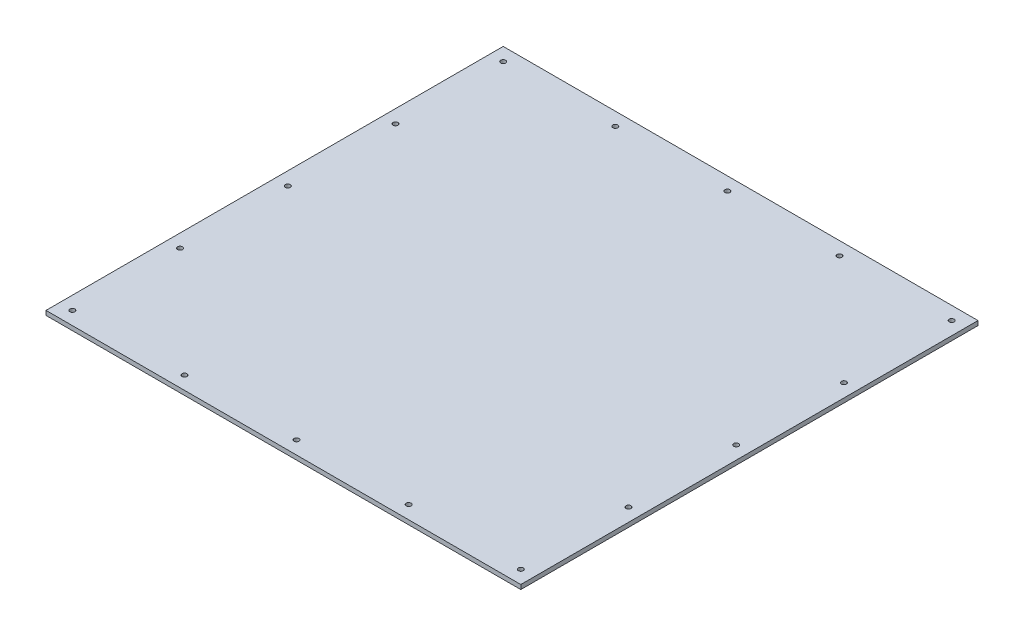
SolidWorks part; units mm, degrees
material "6061 Alloy"
ref_plane "Front Plane" through (0, 0, 0) normal (0, 0, 1) x (1, 0, 0)
ref_plane "Top Plane" through (0, 0, 0) normal (0, 1, 0) x (1, 0, 0)
ref_plane "Right Plane" through (0, 0, 0) normal (1, 0, 0) x (0, 0, -1)
sketch "8020 Reference" plane through (0, 0, 0) normal (0, 1, 0) x (1, 0, 0)
  line L0 (647.7, 0) -> (685.8, 0) construction
  line L1 (0, 0) -> (38.1, 0) construction
  line L2 (0, 0) -> (0, -38.1) construction
  line L3 (0, -38.1) -> (38.1, -38.1) construction
  line L4 (38.1, 0) -> (38.1, -38.1) construction
  line L5 (647.7, 0) -> (647.7, -38.1) construction
  line L6 (647.7, -38.1) -> (685.8, -38.1) construction
  line L7 (685.8, 0) -> (685.8, -38.1) construction
  line L8 (0, -622.3) -> (38.1, -622.3) construction
  line L9 (0, -622.3) -> (0, -660.4) construction
  line L10 (0, -660.4) -> (38.1, -660.4) construction
  line L11 (38.1, -622.3) -> (38.1, -660.4) construction
  line L12 (647.7, -622.3) -> (685.8, -622.3) construction
  line L13 (647.7, -622.3) -> (647.7, -660.4) construction
  line L14 (647.7, -660.4) -> (685.8, -660.4) construction
  line L15 (685.8, -622.3) -> (685.8, -660.4) construction
  circle A0 centre (19.05, -19.05) radius 3.57 construction
  circle A1 centre (666.75, -19.05) radius 3.57 construction
  circle A2 centre (19.05, -641.35) radius 3.57 construction
  circle A3 centre (666.75, -641.35) radius 3.57 construction
  point P8 (19.05, 0)
  point P9 (0, -19.05)
  point P15 (666.75, 0)
  point P16 (647.7, -19.05)
  point P24 (19.05, -622.3)
  point P25 (0, -641.35)
  point P32 (666.75, -622.3)
  point P33 (647.7, -641.35)
  dimension "D2" = 7.14
  dimension "D4" = 7.14
  dimension "D7" = 7.14
  dimension "D9" = 7.14
  dimension "D1" = 38.1
  dimension "D3" = 38.1
  dimension "D5" = 685.8
  dimension "D6" = 38.1
  dimension "D8" = 38.1
  dimension "D10" = 660.4
sketch "Sketch2" plane through (0, 0, 0) normal (0, 1, 0) x (1, 0, 0)
  line L0 (19.05, -19.05) -> (19.05, -641.35) construction
  line L1 (0, 0) -> (685.8, 0)
  line L2 (0, 0) -> (0, -660.4)
  line L3 (0, -660.4) -> (685.8, -660.4)
  line L4 (685.8, 0) -> (685.8, -660.4)
  line L5 (19.05, -641.35) -> (666.75, -641.35) construction
  line L6 (666.75, -641.35) -> (666.75, -19.05) construction
  line L7 (666.75, -19.05) -> (19.05, -19.05) construction
  line L8 (180.975, -19.05) -> (180.975, -641.35) construction
  line L9 (19.05, -174.625) -> (666.75, -174.625) construction
  line L10 (666.75, -485.775) -> (19.05, -485.775) construction
  line L11 (504.825, -19.05) -> (504.825, -641.35) construction
  line L12 (342.9, -19.05) -> (19.05, -19.05) construction
  circle A0 centre (19.05, -19.05) radius 3.57
  circle A1 centre (666.75, -19.05) radius 3.57
  circle A2 centre (666.75, -641.35) radius 3.57
  circle A3 centre (19.05, -641.35) radius 3.57
  circle A4 centre (342.9, -19.05) radius 3.57
  circle A5 centre (19.05, -330.2) radius 3.57
  circle A6 centre (342.9, -641.35) radius 3.57
  circle A7 centre (666.75, -330.2) radius 3.57
  circle A8 centre (180.975, -19.05) radius 3.57
  circle A9 centre (504.825, -19.05) radius 3.57
  circle A10 centre (666.75, -174.625) radius 3.57
  circle A11 centre (19.05, -174.625) radius 3.57
  circle A12 centre (19.05, -485.775) radius 3.57
  circle A13 centre (666.75, -485.775) radius 3.57
  circle A14 centre (504.825, -641.35) radius 3.57
  circle A15 centre (180.975, -641.35) radius 3.57
  dimension "D1" = 7.14
  dimension "D2" = 161.925
  dimension "D3" = 161.925
  dimension "D4" = 323.85
  dimension "D5" = 311.15
  dimension "D6" = 155.575
  dimension "D7" = 155.575
extrude "Boss-Extrude1" add sketch "Sketch2" along normal blind 6.35
equation "\"D3@Sketch2\"=\"D2@Sketch2\""
equation "\"D2@Sketch2\"=\"D4@Sketch2\"/2"
equation "\"D6@Sketch2\"=\"D5@Sketch2\"/2"
equation "\"D7@Sketch2\"=\"D6@Sketch2\""
